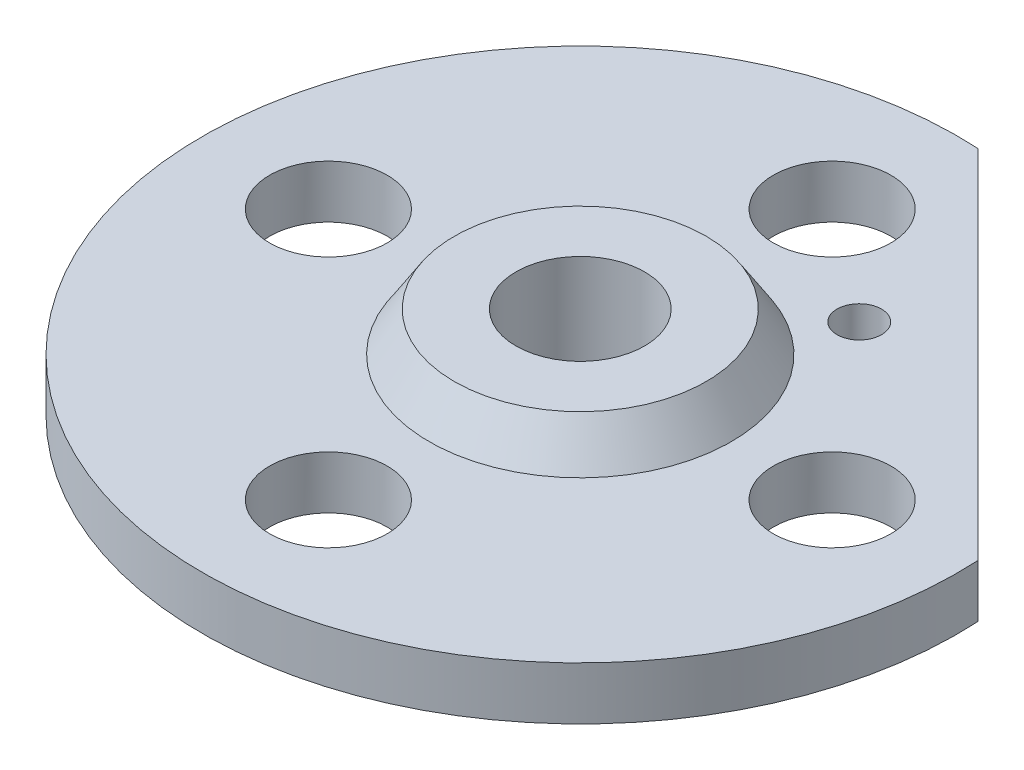
SolidWorks part; units mm, degrees
ref_plane "Ebene vorne" through (0, 0, 0) normal (0, 0, 1) x (1, 0, 0)
ref_plane "Ebene oben" through (0, 0, 0) normal (0, 1, 0) x (1, 0, 0)
ref_plane "Ebene rechts" through (0, 0, 0) normal (1, 0, 0) x (0, 0, -1)
sketch "Skizze1" plane through (0, 0, 0) normal (0, 0, 1) x (1, 0, 0)
  line L0 (0, 0) -> (0, 23.0765) construction
  line L1 (15, 12) -> (0, 12)
  line L2 (15, 12) -> (18, 7.3)
  line L3 (18, 7.3) -> (45, 7.3)
  line L4 (45, 7.3) -> (45, 1)
  line L5 (45, 1) -> (21, 1)
  line L6 (21, 1) -> (20, 0)
  line L7 (0, 12) -> (0, 0)
  line L8 (0, 0) -> (20, 0)
  dimension "D2" = 135
  dimension "D3" = 15
  dimension "D4" = 1
  dimension "D5" = 7.3
  dimension "D6" = 12
  dimension "D7" = 20
  dimension "D8" = 45
  dimension "D10" = 27
revolve "Rotation1" add sketch "Skizze1" angle 360 about L0
sketch "Skizze10" plane through (0, 7.3, 0) normal (0, 1, 0) x (1, 0, 0)
  line L0 (0, 0) -> (0, 30) construction
  circle A0 centre (0, 0) radius 30 construction
  dimension "D1" = 60
hole_wizard "Ø14.0 (14) Durchmesser Bohrung2" positions "Skizze12" profile "Skizze11" hole size "Ø14.0" standard "DIN" end condition through all
sketch "Skizze12" plane through (0, 7.3, 0) normal (0, 1, 0) x (1, 0, 0)
  point P0 (0, 30)
sketch "Skizze11" plane through (0, 7.3, -30) normal (1, 0, 0) x (0, 0, 1)
  line L0 (0, 0) -> (0, 7.3)
  line L1 (0, 7.3) -> (7, 7.3)
  line L2 (7, 7.3) -> (7, 0)
  line L5 (7, 0) -> (0, 0)
  line L11 (0, -6.35) -> (0, 107.95) construction
  dimension "Bohrerdurchmesser" = 14
  dimension "Bohrungstiefe" = 7.3
pattern_circular "Kreismuster2" count 4 over 360 about axis through (0, 0, 0) along (0, 1, 0) of "Ø14.0 (14) Durchmesser Bohrung2"
hole_wizard "3/8-18 NPSM Gewindebohrung1" positions "Skizze14" profile "Skizze15" tap size "3/8-18 NPSM" standard "ANSI Zoll" end condition through all
sketch "Skizze14" plane through (0, 12, 0) normal (0, 1, 0) x (1, 0, 0)
  point P0 (0, 0)
sketch "Skizze15" plane through (0, 12, 0) normal (1, 0, 0) x (0, 0, 1)
  line L0 (0, 0) -> (0, 12)
  line L1 (0, 12) -> (7.6581, 12)
  line L2 (7.6581, 12) -> (7.6581, 0)
  line L5 (7.6581, 0) -> (0, 0)
  line L11 (0, -6.35) -> (0, 107.95) construction
  dimension "Bohrerdurchmesser" = 15.3162
  dimension "Bohrungstiefe" = 12
cosmetic thread "Bohrungsgewinde1" parameters "D2"=16.8148
sketch "Skizze16" plane through (0, 7.3, 0) normal (0, 1, 0) x (1, 0, 0)
  line L0 (44.9337, 2.4425) -> (2.4425, 44.9337)
  line L1 (0, 0) -> (0, 30) construction
  circle A0 centre (0, 0) radius 45 construction
  arc A1 (2.4425, 44.9337) -> (44.9337, 2.4425) centre (0, 0) cw
  dimension "D1" = 45
  dimension "D2" = 45
  dimension "D3" = 33.5
extrude "Schnitt-Linear austragen1" cut sketch "Skizze16" against normal up to surface (6.3 mm away) up to face at (-30, 1, -7)
sketch "Skizze17" plane through (0, 7.3, 0) normal (0, 1, 0) x (1, 0, 0)
  line L0 (34.4685, 12.9077) -> (20.3263, 27.0498)
  line L1 (20.3263, 27.0498) -> (13.2553, 19.9787)
  line L2 (34.4685, 12.9077) -> (27.3974, 5.8366)
  line L3 (2.4425, 44.9337) -> (44.9337, 2.4425) construction
  dimension "D1" = 20
  dimension "D2" = 10
  dimension "D3" = 10
  dimension "D4" = 90
  dimension "D5" = 0
  dimension "D6" = 14.8
hole_wizard "Ø5.3 (5.3) Durchmesser Bohrung1" positions "Skizze19" profile "Skizze18" hole size "Ø5.3" standard "ANSI Metrisch" end condition through all
sketch "Skizze19" plane through (0, 7.3, 0) normal (0, 1, 0) x (1, 0, 0)
  point P0 (13.2553, 19.9787)
sketch "Skizze18" plane through (13.2553, 7.3, -19.9787) normal (1, 0, 0) x (0, 0, 1)
  line L0 (0, 0) -> (0, 7.3)
  line L1 (0, 7.3) -> (2.65, 7.3)
  line L2 (2.65, 7.3) -> (2.65, 0)
  line L5 (2.65, 0) -> (0, 0)
  line L11 (0, -6.35) -> (0, 107.95) construction
  dimension "Bohrerdurchmesser" = 5.3
  dimension "Bohrungstiefe" = 7.3
